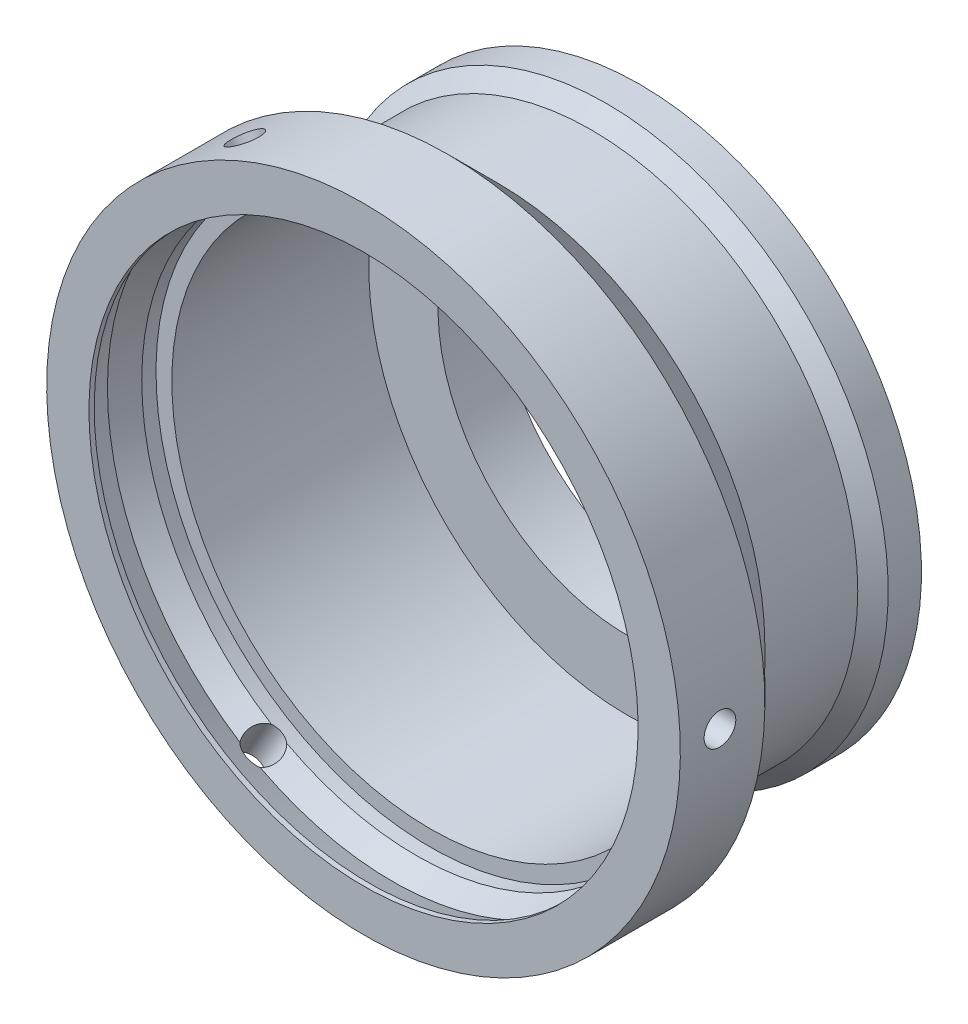
SolidWorks part; units mm, degrees
material "1060 slitina"
ref_plane "Přední rovina" through (0, 0, 0) normal (0, 0, 1) x (1, 0, 0)
ref_plane "Horní rovina" through (0, 0, 0) normal (0, 1, 0) x (1, 0, 0)
ref_plane "Pravá rovina" through (0, 0, 0) normal (1, 0, 0) x (0, 0, -1)
sketch "Skica2" plane through (0, 0, 0) normal (1, 0, 0) x (0, 0, -1)
  line L0 (0, 0) -> (-119.0788, 0) construction
  line L1 (-14.96, 17.955) -> (-14.96, 19.305)
  line L2 (-14.96, 19.305) -> (-15.46, 19.805)
  line L3 (-15.46, 19.805) -> (-16.3, 19.805)
  line L4 (-16.3, 19.805) -> (-16.3, 19.155)
  line L5 (-16.3, 19.155) -> (-18.3, 19.155)
  line L6 (-18.3, 19.155) -> (-18.3, 20.5)
  line L7 (-18.3, 20.5) -> (-19.3, 20.5)
  line L8 (-19.3, 20.5) -> (-19.3, 26.67)
  line L9 (-19.3, 26.67) -> (-22.45, 26.67)
  line L10 (-22.45, 26.67) -> (-23.89, 25.23)
  line L11 (-23.89, 25.23) -> (-32.69, 25.23)
  line L12 (-32.69, 25.23) -> (-37.46, 30)
  line L13 (-37.46, 30) -> (-45.46, 30)
  line L14 (-45.46, 30) -> (-45.46, 26)
  line L15 (-14.96, 17.955) -> (-20.46, 17.955)
  line L16 (-20.46, 17.955) -> (-20.46, 24.5)
  line L17 (-20.46, 24.5) -> (-39.11, 24.5)
  line L18 (-39.11, 24.5) -> (-39.11, 26)
  line L19 (-39.11, 26) -> (-40.46, 26)
  line L20 (-40.46, 26) -> (-42.71, 27)
  line L21 (-42.71, 27) -> (-44.96, 26)
  line L22 (-44.96, 26) -> (-45.46, 26)
  dimension "D1" = 53.34
  dimension "D2" = 50.46
  dimension "D3" = 60
  dimension "D4" = 30.5
  dimension "D5" = 8
  dimension "D6" = 8.8
  dimension "D7" = 45.46
  dimension "D8" = 26.16
  dimension "D9" = 1
  dimension "D10" = 41
  dimension "D11" = 38.31
  dimension "D12" = 1.2
  dimension "D13" = 1.85
  dimension "D14" = 2
  dimension "D15" = 1.34
  dimension "D16" = 4.34
  dimension "D17" = 45
  dimension "D18" = 0.5
  dimension "D19" = 35.91
  dimension "D20" = 25
  dimension "D21" = 49
  dimension "D22" = 6.35
  dimension "D23" = 5
  dimension "D24" = 0.5
  dimension "D25" = 52
  dimension "D26" = 1
  dimension "D27" = 19.3
revolve "Rotovat1" add sketch "Skica2" angle 360 about L0
sketch "Skica3" plane through (0, 0, 0) normal (1, 0, 0) x (0, 0, -1)
  line L0 (-45.46, 30) -> (-45.46, -30) construction
  line L1 (-37.46, 30) -> (-37.46, -30) construction
  line L2 (-20.46, 17.955) -> (-20.46, -17.955) construction
  circle A0 centre (-41.71, 0) radius 1.25 construction
  circle A1 centre (-41.71, 0) radius 1.5
  dimension "D1" = 3
  dimension "D2" = 2.5
  dimension "D3" = 3
  dimension "D5" = 21.25
  dimension "D4" = 3.75
extrude "Odebrat vysunutím1" cut sketch "Skica3" along normal up to next
pattern_circular "Kruhové pole1" count 3 over 360 about axis through (0, 0, 0) along (0, 0, -1) of "Odebrat vysunutím1"
sketch "Skica4" plane through (0, 0, 19.3) normal (0, 0, -1) x (-1, 0, 0)
  circle A0 centre (0, 24.27) radius 1
  circle A1 centre (0, 0) radius 26.67 construction
  dimension "D1" = 2
  dimension "D2" = 1.4
extrude "Odebrat vysunutím2" cut sketch "Skica4" against normal blind 0.25
